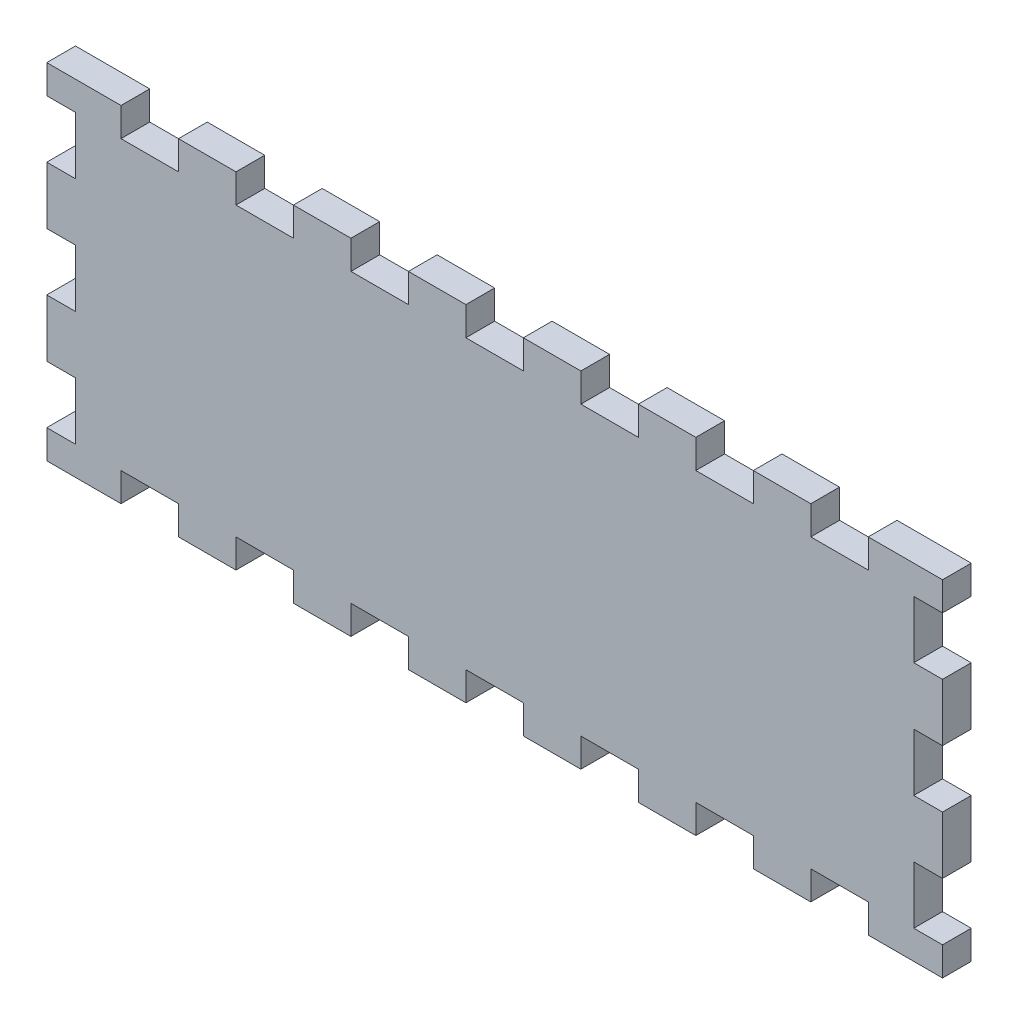
SolidWorks part; units mm, degrees
ref_plane "Front Plane" through (0, 0, 0) normal (0, 0, 1) x (1, 0, 0)
ref_plane "Top Plane" through (0, 0, 0) normal (0, 1, 0) x (1, 0, 0)
ref_plane "Right Plane" through (0, 0, 0) normal (1, 0, 0) x (0, 0, -1)
sketch "Sketch1" plane through (0, 0, 0) normal (0, 0, 1) x (1, 0, 0)
  line L0 (-93.5, 6) -> (-78, 6)
  line L1 (-78, 6) -> (-78, 0)
  line L2 (-78, 0) -> (-66, 0)
  line L3 (-66, 0) -> (-66, 6)
  line L4 (-66, 6) -> (-54, 6)
  line L5 (-54, 6) -> (-54, 0)
  line L6 (-54, 0) -> (-42, 0)
  line L7 (-42, 0) -> (-42, 6)
  line L8 (-42, 6) -> (-30, 6)
  line L9 (-30, 6) -> (-30, 0)
  line L10 (-30, 0) -> (-18, 0)
  line L11 (-18, 0) -> (-18, 6)
  line L12 (-18, 6) -> (-6, 6)
  line L13 (-6, 6) -> (-6, 0)
  line L14 (-6, 0) -> (6, 0)
  line L15 (6, 0) -> (6, 6)
  line L16 (6, 6) -> (18, 6)
  line L17 (18, 6) -> (18, 0)
  line L18 (18, 0) -> (30, 0)
  line L19 (30, 0) -> (30, 6)
  line L20 (30, 6) -> (42, 6)
  line L21 (42, 6) -> (42, 0)
  line L22 (42, 0) -> (54, 0)
  line L23 (54, 0) -> (54, 6)
  line L24 (54, 6) -> (66, 6)
  line L25 (66, 6) -> (66, 0)
  line L26 (66, 0) -> (78, 0)
  line L27 (78, 0) -> (78, 6)
  line L28 (78, 6) -> (93.5, 6)
  line L29 (93.5, 6) -> (93.5, 0)
  line L30 (93.5, 0) -> (87.5, 0)
  line L31 (87.5, 0) -> (87.5, -12)
  line L32 (87.5, -12) -> (93.5, -12)
  line L33 (93.5, -12) -> (93.5, -24)
  line L34 (93.5, -24) -> (87.5, -24)
  line L35 (87.5, -24) -> (87.5, -36)
  line L36 (87.5, -36) -> (93.5, -36)
  line L37 (93.5, -36) -> (93.5, -48)
  line L38 (93.5, -48) -> (87.5, -48)
  line L39 (87.5, -48) -> (87.5, -60)
  line L40 (87.5, -60) -> (93.5, -60)
  line L41 (93.5, -60) -> (93.5, -66)
  line L42 (93.5, -66) -> (78, -66)
  line L43 (78, -66) -> (78, -60)
  line L44 (78, -60) -> (66, -60)
  line L45 (66, -60) -> (66, -66)
  line L46 (66, -66) -> (54, -66)
  line L47 (54, -66) -> (54, -60)
  line L48 (54, -60) -> (42, -60)
  line L49 (42, -60) -> (42, -66)
  line L50 (42, -66) -> (30, -66)
  line L51 (30, -66) -> (30, -60)
  line L52 (30, -60) -> (18, -60)
  line L53 (18, -60) -> (18, -66)
  line L54 (18, -66) -> (6, -66)
  line L55 (6, -66) -> (6, -60)
  line L56 (6, -60) -> (-6, -60)
  line L57 (-6, -60) -> (-6, -66)
  line L58 (-6, -66) -> (-18, -66)
  line L59 (-18, -66) -> (-18, -60)
  line L60 (-18, -60) -> (-30, -60)
  line L61 (-30, -60) -> (-30, -66)
  line L62 (-30, -66) -> (-42, -66)
  line L63 (-42, -66) -> (-42, -60)
  line L64 (-42, -60) -> (-54, -60)
  line L65 (-54, -60) -> (-54, -66)
  line L66 (-54, -66) -> (-66, -66)
  line L67 (-66, -66) -> (-66, -60)
  line L68 (-66, -60) -> (-78, -60)
  line L69 (-78, -60) -> (-78, -66)
  line L70 (-78, -66) -> (-93.5, -66)
  line L71 (-93.5, -66) -> (-93.5, -60)
  line L72 (-93.5, -60) -> (-87.5, -60)
  line L73 (-87.5, -60) -> (-87.5, -48)
  line L74 (-87.5, -48) -> (-93.5, -48)
  line L75 (-93.5, -48) -> (-93.5, -36)
  line L76 (-93.5, -36) -> (-87.5, -36)
  line L77 (-87.5, -36) -> (-87.5, -24)
  line L78 (-87.5, -24) -> (-93.5, -24)
  line L79 (-93.5, -24) -> (-93.5, -12)
  line L80 (-93.5, -12) -> (-87.5, -12)
  line L81 (-87.5, -12) -> (-87.5, 0)
  line L82 (-87.5, 0) -> (-93.5, 0)
  line L83 (-93.5, 0) -> (-93.5, 6)
extrude "Boss-Extrude1" add sketch "Sketch1" along normal blind 6 contours L83 L0 L1 L2 L3 L4 L5 L6 L7 L8 L9 L10 L11 L12 L13 L14 L15 L16 L17 L18 L19 L20 L21 L22 L23 L24 L25 L26 L27 L28 L29 L30 L31 L32 L33 L34 L35 L36 L37 L38 L39 L40 L41 L42 L43 L44 L45 L46 L47 L48 L49 L50 L51 L52 L53 L54 L55 L56 L57 L58 L59 L60 L61 L62 L63 L64 L65 L66 L67 L68 L69 L70 L71 L72 L73 L74 L75 L76 L77 L78 L79 L80 L81 L82
